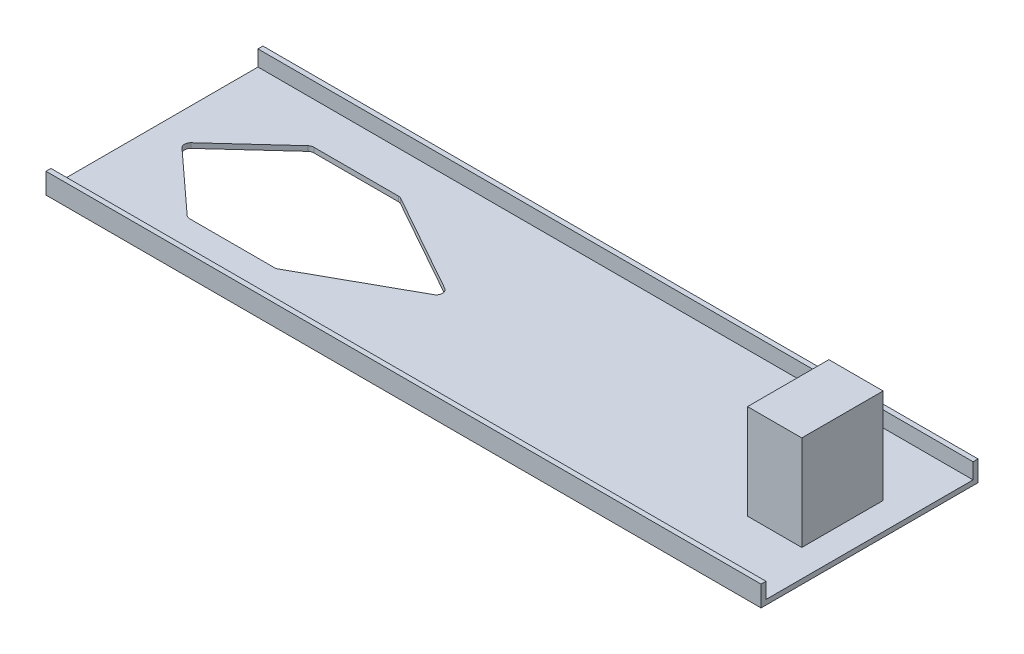
SolidWorks part; units mm, degrees
material "6061-T6 (SS)"
ref_plane "Front Plane" through (0, 0, 0) normal (0, 0, 1) x (1, 0, 0)
ref_plane "Top Plane" through (0, 0, 0) normal (0, 1, 0) x (1, 0, 0)
ref_plane "Right Plane" through (0, 0, 0) normal (1, 0, 0) x (0, 0, -1)
sketch "Sketch1" plane through (0, 0, 0) normal (0, 1, 0) x (1, 0, 0)
  line L1 (0, 0) -> (669.925, 0)
  line L2 (0, 0) -> (0, 203.2)
  line L3 (0, 203.2) -> (669.925, 203.2)
  line L4 (669.925, 0) -> (669.925, 203.2)
  dimension "D1" = 203.2
  dimension "D2" = 669.925
extrude "Boss-Extrude1" add sketch "Sketch1" along normal blind 4.6228
sketch "Sketch2" plane through (0, 4.6228, 0) normal (0, 1, 0) x (1, 0, 0)
  line L0 (669.925, 0) -> (669.925, 203.2) construction
  line L1 (0, 0) -> (669.925, 0)
  line L2 (0, 0) -> (0, 4.6228)
  line L3 (0, 4.6228) -> (669.925, 4.6228)
  line L4 (669.925, 0) -> (669.925, 4.6228)
  line L5 (0, 203.2) -> (0, 0) construction
  line L6 (669.925, 203.2) -> (0, 203.2)
  line L7 (669.925, 203.2) -> (669.925, 198.5772)
  line L8 (669.925, 198.5772) -> (0, 198.5772)
  line L9 (0, 203.2) -> (0, 198.5772)
  dimension "D1" = 4.6228
  dimension "D2" = 4.6228
extrude "Boss-Extrude2" add sketch "Sketch2" along normal blind 14.732
sketch "Sketch3" plane through (0, 4.6228, 0) normal (0, 1, 0) x (1, 0, 0)
  line L0 (171.958, 159.7025) -> (171.958, 43.4975) construction
  line L1 (0, 198.5772) -> (0, 4.6228) construction
  line L2 (0, 101.6) -> (25.4, 101.6) construction
  line L3 (171.958, 43.4975) -> (88.9, 43.4975)
  line L4 (171.958, 159.7025) -> (88.9, 159.7025)
  line L5 (171.958, 159.7025) -> (276.225, 101.3968)
  line L6 (276.225, 101.3968) -> (171.958, 43.4975)
  line L7 (88.9, 159.7025) -> (25.4, 101.6)
  line L8 (25.4, 101.6) -> (88.9, 43.4975)
  point P4 (171.958, 101.6)
  point P5 (0, 101.6)
  dimension "D1" = 116.205
  dimension "D2" = 25.4
  dimension "D3" = 83.058
  dimension "D4" = 83.058
  dimension "D5" = 88.9
  dimension "D6" = 276.225
extrude "Cut-Extrude1" cut sketch "Sketch3" against normal through all
fillet "Fillet1" radius 5.842 6 edges at (276.225, 2.3114, -101.3968) (171.958, 2.3114, -43.4975) (88.9, 2.3114, -43.4975) (25.4, 2.3114, -101.6) (88.9, 2.3114, -159.7025) (171.958, 2.3114, -159.7025)
sketch "Sketch4" plane through (0, 4.6228, 0) normal (0, 1, 0) x (1, 0, 0)
  line L0 (669.925, 4.6228) -> (669.925, 198.5772) construction
  line L1 (644.525, 139.7) -> (593.725, 139.7)
  line L2 (644.525, 139.7) -> (644.525, 63.5)
  line L3 (644.525, 63.5) -> (593.725, 63.5)
  line L4 (593.725, 139.7) -> (593.725, 63.5)
  point P6 (644.525, 101.6)
  point P7 (669.925, 101.6)
  dimension "D1" = 25.4
  dimension "D2" = 76.2
  dimension "D3" = 50.8
extrude "Boss-Extrude3" add sketch "Sketch4" along normal blind 88.9
